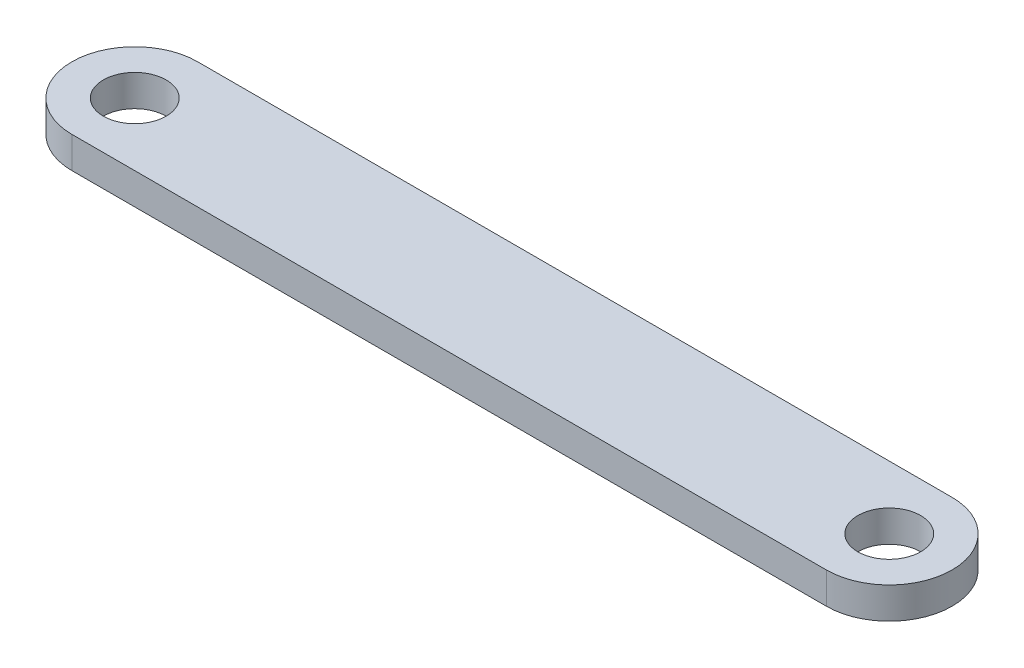
SolidWorks part; units mm, degrees
ref_plane "Front Plane" through (0, 0, 0) normal (0, 0, 1) x (1, 0, 0)
ref_plane "Top Plane" through (0, 0, 0) normal (0, 1, 0) x (1, 0, 0)
ref_plane "Right Plane" through (0, 0, 0) normal (1, 0, 0) x (0, 0, -1)
sketch "Sketch2" plane through (0, 0, 0) normal (0, 1, 0) x (1, 0, 0)
  line L0 (-60, 0) -> (60, 0) construction
  line L1 (-60, 10) -> (60, 10)
  line L2 (-60, -10) -> (60, -10)
  arc A0 (-60, 10) -> (-60, -10) centre (-60, 0) ccw
  arc A1 (60, -10) -> (60, 10) centre (60, 0) ccw
  circle A2 centre (-60, 0) radius 5
  circle A3 centre (60, 0) radius 5
  point P2 (0, 0)
  dimension "D3" = 10
  dimension "D4" = 10
  dimension "D1" = 120
  dimension "D2" = 20
extrude "Boss-Extrude1" add sketch "Sketch2" along normal blind 5
